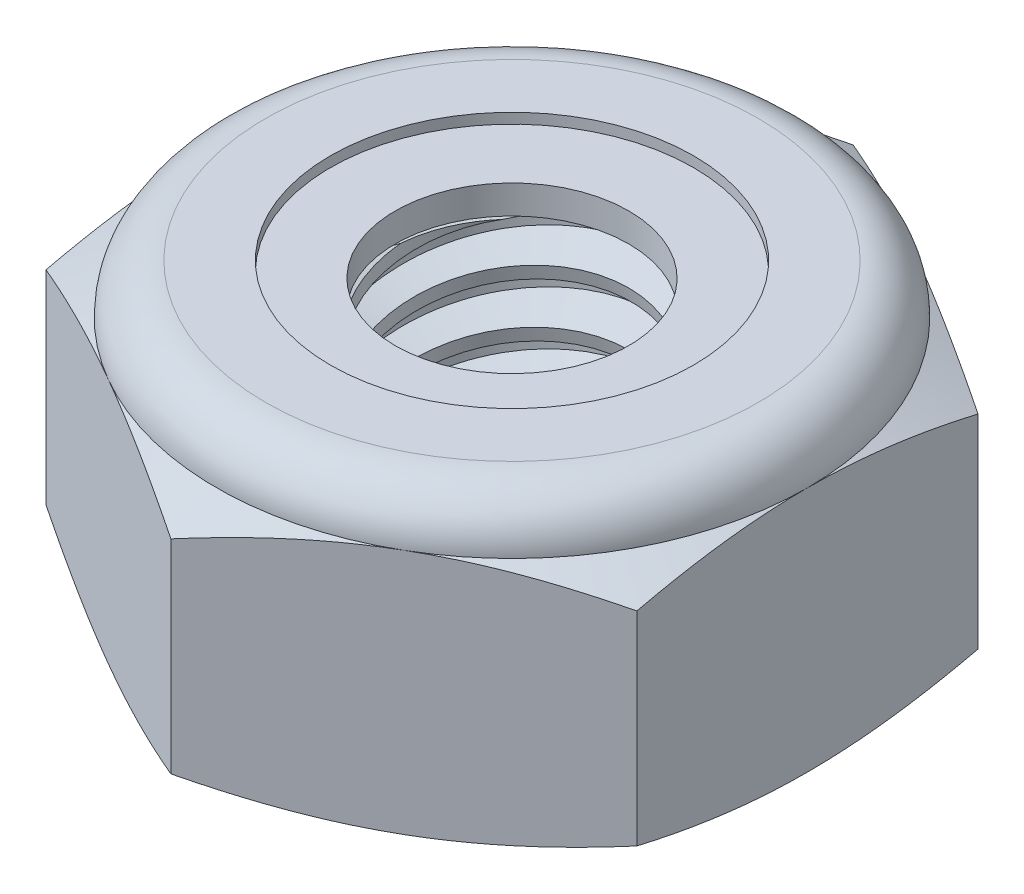
SolidWorks part; units mm, degrees
material "Alloy Steel"
ref_plane "Front" through (0, 0, 0) normal (0, 0, 1) x (1, 0, 0)
ref_plane "Top" through (0, 0, 0) normal (0, 1, 0) x (1, 0, 0)
ref_plane "Right" through (0, 0, 0) normal (1, 0, 0) x (0, 0, -1)
sketch "Sketch1" plane through (0, 0, 0) normal (0, 1, 0) x (1, 0, 0)
  line L1 (0, 5.041) -> (-4.3656, 2.5205)
  line L2 (-4.3656, 2.5205) -> (-4.3656, -2.5205)
  line L3 (-4.3656, -2.5205) -> (0, -5.041)
  line L4 (0, -5.041) -> (4.3656, -2.5205)
  line L5 (4.3656, -2.5205) -> (4.3656, 2.5205)
  line L6 (4.3656, 2.5205) -> (0, 5.041)
  circle A0 centre (0, 0) radius 4.3656 construction
  dimension "Hex Flats" = 8.7312
extrude "Extrude1" add sketch "Sketch1" along normal blind 4.3656
sketch "Sketch2" plane through (0, 0, 0) normal (1, 0, 0) x (0, 0, -1)
  line L0 (-2.0828, 0) -> (-2.0828, 4.3656) construction
  line L1 (0, 0) -> (2.0828, 0)
  line L2 (0, 0) -> (0, 4.3656)
  line L3 (0, 4.3656) -> (2.0828, 4.3656)
  line L4 (2.0828, 0) -> (2.0828, 4.3656)
  line L5 (-2.5205, 4.3656) -> (2.5205, 4.3656) construction
  line L7 (0, -2.0828) -> (0, 0) construction
  dimension "Thread Dia" = 4.1656
revolve "Revolve1" add sketch "Sketch2" angle 360 about L7
sketch "Sketch3" plane through (0, 0, 0) normal (1, 0, 0) x (0, 0, -1)
  line L0 (2.0828, 4.3656) -> (-2.0828, 4.3656) construction
  line L1 (-2.0828, 4.3656) -> (-2.0828, 3.5719) construction
  line L2 (-2.0828, 3.5719) -> (2.0828, 4.3656) construction
  line L3 (2.0828, 4.3656) -> (2.1014, 4.2682) construction
  line L4 (2.1014, 4.2682) -> (2.2314, 3.5859)
  line L5 (2.2314, 3.5859) -> (1.7629, 3.7491)
  line L6 (1.7629, 3.7491) -> (1.7258, 3.9441)
  line L7 (1.7258, 3.9441) -> (2.1014, 4.2682)
  line L8 (1.7443, 3.8466) -> (2.1664, 3.927) construction
  line L9 (2.0828, 4.3656) -> (2.0828, 3.9111) construction
  line L10 (2.0828, 3.9111) -> (-2.0828, 3.1174) construction
  line L11 (-2.0828, 3.1174) -> (-2.0828, 3.5719) construction
  line L12 (-0.1622, 4.3656) -> (0.1622, 2.6628) construction
  line L13 (-2.0828, 0) -> (-2.0828, 4.3656) construction
  line L14 (0, 4.3656) -> (2.0828, 4.3656) construction
  line L15 (2.0828, 0) -> (2.0828, 4.3656) construction
  point P13 (0, 3.5142)
  dimension "D1" = 0.0992
  dimension "D2" = 0.1984
  dimension "Thread Pitch" = 0.7937
  dimension "D4" = 60
  dimension "D5" = 0.7937
revolve "Cut-Revolve1" cut sketch "Sketch3" angle 360 about L12
pattern_linear "LPattern1" count 6 spacing 0.7937 along (0, -1, 0) count 2 spacing 0.7937 along (0, 1, 0) of "Cut-Revolve1"
sketch "Sketch4" plane through (0, 0, 0) normal (1, 0, 0) x (0, 0, -1)
  line L0 (0, 4.3656) -> (2.0828, 4.3656)
  line L1 (2.0828, 4.3656) -> (1.7258, 4.1991)
  line L2 (1.7258, 4.1991) -> (1.7258, 0.1665)
  line L3 (1.7258, 0.1665) -> (2.0828, 0)
  line L4 (2.0828, 0) -> (0, 0)
  line L5 (0, 0) -> (0, 4.3656)
  line L6 (2.0828, 0) -> (2.0828, 4.3656) construction
  line L7 (0, 4.3656) -> (2.0828, 4.3656) construction
  line L8 (0, 0) -> (2.0828, 0) construction
  line L9 (0, 0) -> (0, 4.3656) construction
  line L10 (0, 4.3656) -> (0, 4.7596) construction
  dimension "D1" = 25
revolve "Cut-Revolve2" cut sketch "Sketch4" angle 360 about L10
combine bodies "Combine1" operation type subtract main body 112 bodies to subtract 111
sketch "Sketch5" plane through (0, 0, 0) normal (1, 0, 0) x (0, 0, -1)
  line L0 (0, 0) -> (4.3656, 0)
  line L1 (4.3656, 0) -> (5.041, 0.3149)
  line L2 (5.041, 0.3149) -> (5.041, 3.3231)
  line L3 (5.041, 3.3231) -> (4.3656, 3.638)
  line L4 (3.638, 4.3656) -> (3.638, 5.6356)
  line L5 (3.638, 5.6356) -> (6.311, 5.6356)
  line L6 (6.311, 5.6356) -> (6.311, -1.27)
  line L7 (6.311, -1.27) -> (0, -1.27)
  line L8 (0, -1.27) -> (0, 0)
  line L9 (4.3656, 3.638) -> (4.3656, 0) construction
  line L10 (0, 0) -> (2.0828, 0) construction
  line L13 (5.041, 1.819) -> (6.311, 1.819) construction
  line L14 (5.041, 4.3656) -> (5.041, 0) construction
  line L15 (0, 0) -> (0, 5.6356) construction
  line L20 (0, 5.6356) -> (3.638, 5.6356) construction
  line L22 (0, 4.3656) -> (2.0828, 4.3656) construction
  arc A0 (4.3656, 3.638) -> (3.638, 4.3656) centre (3.638, 3.638) ccw
  dimension "D1" = 25
  dimension "D2" = 1.27
  dimension "D3" = 4.3656
  dimension "D4" = 0.7276
revolve "Cut-Revolve3" cut sketch "Sketch5" angle 360 about L15
sketch "Sketch6" plane through (0, 0, 0) normal (1, 0, 0) x (0, 0, -1)
  line L0 (0, 3.638) -> (4.2132, 3.638)
  line L1 (3.638, 4.2132) -> (2.6819, 4.2132)
  line L2 (0, 5.6356) -> (0, 3.638)
  line L3 (2.6819, 5.6356) -> (0, 5.6356)
  line L4 (0, 5.6356) -> (3.638, 5.6356) construction
  line L5 (0, 0) -> (0, 5.6356) construction
  line L6 (0, 5.6356) -> (0, 44.323) construction
  line L7 (2.6819, 4.2132) -> (2.6819, 5.6356)
  line L8 (3.638, 4.3656) -> (3.638, 4.2132) construction
  line L9 (2.6819, 4.2132) -> (1.7258, 4.2132) construction
  line L10 (1.7258, 4.2132) -> (1.7258, 4.1991) construction
  arc A0 (4.2132, 3.638) -> (3.638, 4.2132) centre (3.638, 3.638) ccw
  arc A1 (4.3656, 3.638) -> (3.638, 4.3656) centre (3.638, 3.638) ccw construction
  dimension "D1" = 0.1524
revolve "Cut-Revolve4" cut sketch "Sketch6" angle 360 about L6
sketch "Sketch7" plane through (0, 0, 0) normal (1, 0, 0) x (0, 0, -1)
  line L0 (1.7258, 3.7142) -> (4.1312, 3.7142)
  line L1 (3.638, 4.137) -> (1.7258, 4.137)
  line L2 (1.7258, 4.137) -> (1.7258, 3.7142)
  line L3 (1.7258, 3.7142) -> (0, 3.7142) construction
  line L4 (0, 3.7142) -> (0, 4.137) construction
  line L5 (0, 4.137) -> (1.7258, 4.137) construction
  line L6 (1.7258, 3.7142) -> (1.7258, 3.638) construction
  line L7 (0, 3.638) -> (4.2132, 3.638) construction
  line L8 (3.638, 4.137) -> (3.638, 4.2132) construction
  arc A0 (4.1312, 3.7142) -> (3.638, 4.137) centre (3.638, 3.638) ccw
  arc A2 (4.2132, 3.638) -> (3.638, 4.2132) centre (3.638, 3.638) ccw construction
  dimension "D1" = 0.0762
revolve "Revolve2" add sketch "Sketch7" angle 360 about L4
equation "\"D1@Sketch3\"=\"Thread Pitch@Sketch3\"/8"
equation "\"D2@Sketch3\"=\"Thread Pitch@Sketch3\"/4"
equation "\"D5@Sketch3\"=\"Thread Pitch@Sketch3\""
equation "\"D4@LPattern1\"=\"Thread Pitch@Sketch3\""
equation "\"D3@LPattern1\"=\"Thread Pitch@Sketch3\""
equation "\"D1@LPattern1\"=\"Height@Extrude1\"/\"Thread Pitch@Sketch3\""
equation "\"D4@Sketch5\"=\"Height@Extrude1\"/6"
